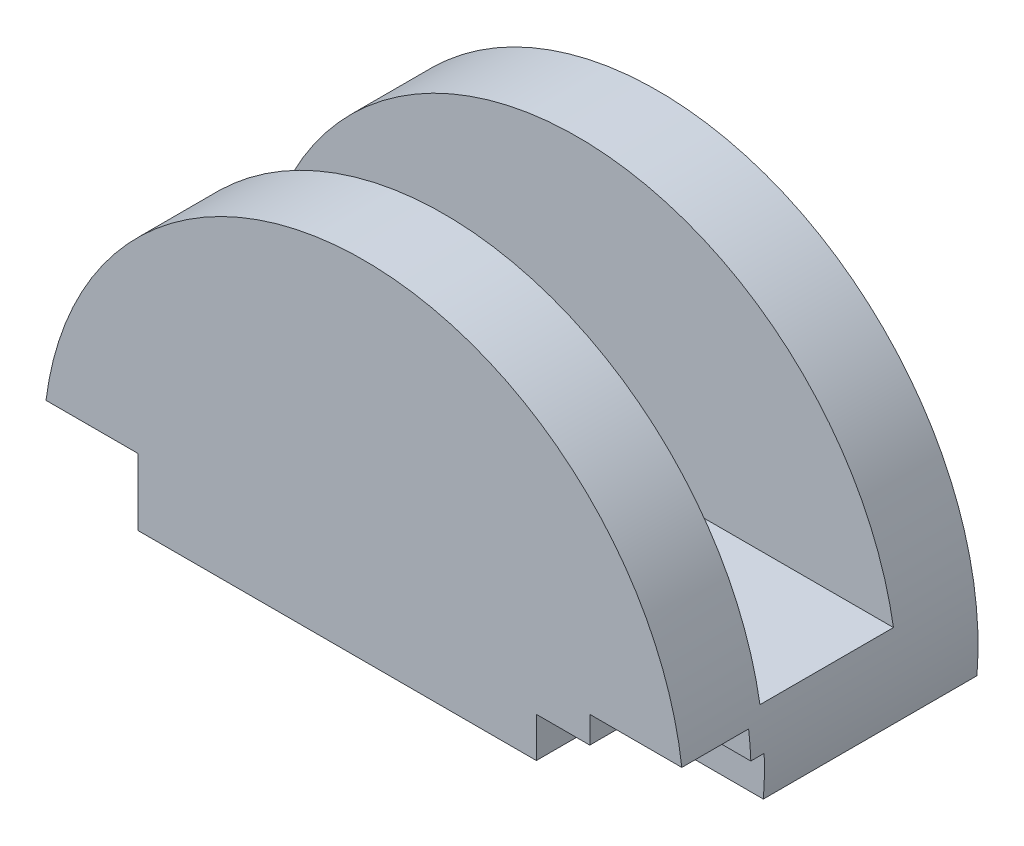
SolidWorks part; units mm, degrees
ref_plane "Front Plane" through (0, 0, 0) normal (0, 0, 1) x (1, 0, 0)
ref_plane "Top Plane" through (0, 0, 0) normal (0, 1, 0) x (1, 0, 0)
ref_plane "Right Plane" through (0, 0, 0) normal (1, 0, 0) x (0, 0, -1)
sketch "Sketch1" plane through (0, 0, 0) normal (0, 0, 1) x (1, 0, 0)
  line L1 (-11.9583, -1) -> (11.9583, -1)
  arc A1 (11.9583, -1) -> (-11.9583, -1) centre (0, 0) ccw
  dimension "D3" = 1
extrude "Boss-Extrude1" add sketch "Sketch1" along normal blind 11
sketch "Sketch2" plane through (0, 2, 0) normal (0, -1, 0) x (1, 0, 0)
  circle A0 centre (0, 5.5) radius 4.25
extrude "Cut-Extrude1" cut sketch "Sketch2" against normal blind 4 from surface at 3 starting at face at (0, -1, 5.5)
sketch "Sketch3" plane through (0, 0, 0) normal (1, 0, 0) x (0, 0, -1)
  line L1 (-8, 2) -> (-3, 2)
  line L2 (-8, 2) -> (-8, 15.4646)
  line L3 (-8, 15.4646) -> (-3, 15.4646)
  line L4 (-3, 2) -> (-3, 15.4646)
  line L5 (0, 2) -> (0, 12) construction
  line L6 (-11, -1) -> (0, -1) construction
  dimension "D1" = 5
  dimension "D2" = 3
  dimension "D3" = 3
extrude "Cut-Extrude2" cut sketch "Sketch3" against normal through all and the other way through all
sketch "Sketch4" plane through (0, 0, 11) normal (0, 0, 1) x (1, 0, 0)
  line L0 (-11.9583, -1) -> (11.9583, -1) construction
  line L1 (6.4583, -1) -> (13.7316, -1)
  line L2 (6.4583, -1) -> (6.4583, 0.5)
  line L3 (6.4583, 0.5) -> (13.7316, 0.5)
  line L4 (13.7316, -1) -> (13.7316, 0.5)
  dimension "D1" = 5.5
  dimension "D2" = 1.5
extrude "Cut-Extrude3" cut sketch "Sketch4" against normal blind 3
sketch "Sketch5" plane through (0, 0, 11) normal (0, 0, 1) x (1, 0, 0)
  line L0 (-11.9583, -1) -> (6.4583, -1) construction
  line L1 (-8.4583, -1) -> (-12.7226, -1)
  line L2 (-8.4583, -1) -> (-8.4583, 1.5)
  line L3 (-8.4583, 1.5) -> (-12.7226, 1.5)
  line L4 (-12.7226, -1) -> (-12.7226, 1.5)
  dimension "D1" = 2.5
  dimension "D2" = 3.5
  dimension "D3" = 0
extrude "Cut-Extrude4" cut sketch "Sketch5" against normal blind 2.5
sketch "Sketch6" plane through (0, 0, 11) normal (0, 0, 1) x (1, 0, 0)
  line L0 (6.4583, -1) -> (11.9583, -1) construction
  line L1 (8.4583, -1) -> (13.6955, -1)
  line L2 (8.4583, -1) -> (8.4583, 1.5)
  line L3 (8.4583, 1.5) -> (13.6955, 1.5)
  line L4 (13.6955, -1) -> (13.6955, 1.5)
  dimension "D1" = 2.5
  dimension "D2" = 3.5
  dimension "D3" = 0
extrude "Cut-Extrude5" cut sketch "Sketch6" against normal blind 2.5
